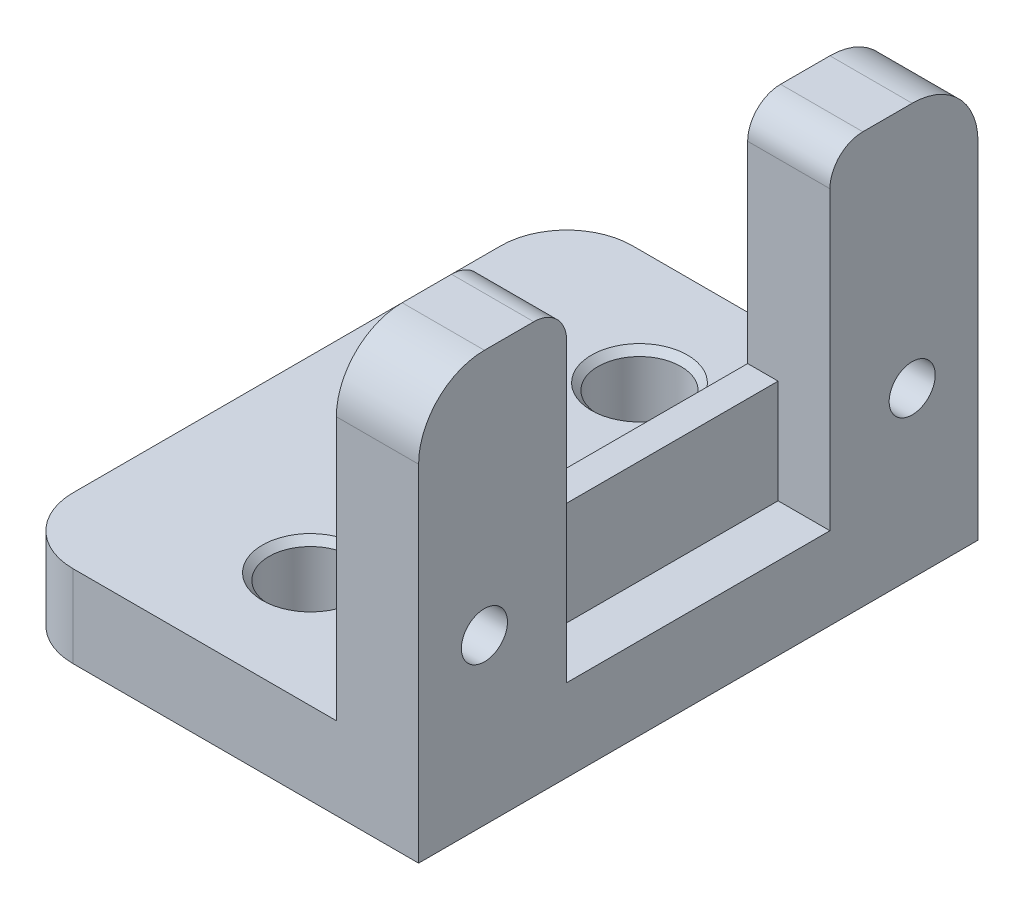
SolidWorks part; units mm, degrees
ref_plane "Plane XZ" through (0, 0, 0) normal (0, 0, 1) x (1, 0, 0)
ref_plane "Plane XY" through (0, 0, 0) normal (0, 1, 0) x (1, 0, 0)
ref_plane "Plane YZ" through (0, 0, 0) normal (1, 0, 0) x (0, 0, -1)
sketch "Sketch1" plane through (0, 0, 0) normal (0, 0, 1) x (1, 0, 0)
  line L0 (-15.875, 0) -> (0, 0)
  line L1 (0, 0) -> (0, 15.875)
  line L2 (0, 15.875) -> (-3.175, 15.875)
  line L3 (-3.175, 15.875) -> (-3.175, 3.175)
  line L4 (-3.175, 3.175) -> (-15.875, 3.175)
  line L5 (-15.875, 3.175) -> (-15.875, 0)
  dimension "D1" = 15.875
  dimension "D2" = 3.175
extrude "Boss-Extrude1" add sketch "Sketch1" along normal mid plane 21.59
sketch "Sketch2" plane through (0, 0, 0) normal (1, 0, 0) x (0, 0, -1)
  line L0 (0, 0) -> (0, 3.175) construction
  line L1 (-10.795, 0) -> (10.795, 0) construction
  line L2 (-10.795, 15.875) -> (10.795, 15.875) construction
  line L3 (-5.08, 15.875) -> (5.08, 15.875)
  line L4 (-5.08, 15.875) -> (-5.08, 3.175)
  line L5 (-5.08, 3.175) -> (5.08, 3.175)
  line L6 (5.08, 15.875) -> (5.08, 3.175)
  line L7 (-10.795, 3.175) -> (10.795, 3.175) construction
  circle A0 centre (-8.255, 6.35) radius 0.889
  circle A1 centre (8.255, 6.35) radius 0.889
  dimension "D1" = 16.51
  dimension "D2" = 1.778
  dimension "D3" = 3.175
  dimension "D4" = 12.7
  dimension "D5" = 10.16
extrude "Cut-Extrude1" cut sketch "Sketch2" against normal through all
sketch "Sketch3" plane through (0, 3.175, 0) normal (0, 1, 0) x (1, 0, 0)
  line L0 (0, 0) -> (-8.62, 0) construction
  line L1 (0, -5.08) -> (0, 5.08) construction
  line L2 (-8.62, 6.35) -> (-8.62, -6.35) construction
  circle A0 centre (-8.62, 6.35) radius 1.6
  circle A1 centre (-8.62, -6.35) radius 1.6
  dimension "D3" = 3.2
  dimension "D1" = 12.7
  dimension "D2" = 8.62
extrude "Cut-Extrude2" cut sketch "Sketch3" against normal through all
ref_plane "Plane1" through (10, 0, 0) normal (1, 0, 0) x (0, 0, -1)
sketch "Sketch4" plane through (0, 3.175, 0) normal (0, 1, 0) x (1, 0, 0)
  line L0 (-8.112, -6.35) -> (-13.192, -6.35) construction
  line L1 (-8.112, -7.95) -> (-13.192, -7.95)
  line L2 (-8.112, -4.75) -> (-13.192, -4.75)
  line L3 (0, 0) -> (-15.875, 0) construction
  line L4 (-15.875, -10.795) -> (-15.875, 10.795) construction
  line L5 (-8.112, 6.35) -> (-13.192, 6.35) construction
  line L6 (-8.112, 7.95) -> (-13.192, 7.95)
  line L7 (-8.112, 4.75) -> (-13.192, 4.75)
  arc A0 (-8.112, -7.95) -> (-8.112, -4.75) centre (-8.112, -6.35) ccw
  arc A1 (-13.192, -4.75) -> (-13.192, -7.95) centre (-13.192, -6.35) ccw
  circle A2 centre (-8.62, -6.35) radius 1.6 construction
  arc A3 (-8.112, 7.95) -> (-8.112, 4.75) centre (-8.112, 6.35) cw
  arc A4 (-13.192, 4.75) -> (-13.192, 7.95) centre (-13.192, 6.35) cw
  point P2 (-10.652, -6.35)
  point P11 (-8.62, -6.35)
  point P18 (-10.652, 6.35)
  dimension "D1" = 0.508
  dimension "D2" = 5.08
  dimension "D3" = 3.2
sketch "Sketch5" plane through (0, 3.175, 0) normal (0, 1, 0) x (1, 0, 0)
  line L0 (-3.175, 5.08) -> (0, 5.08) construction
  line L1 (-3.175, -5.08) -> (-2, -5.08)
  line L2 (-3.175, -5.08) -> (-3.175, 5.08)
  line L3 (-3.175, 5.08) -> (-2, 5.08)
  line L4 (-2, -5.08) -> (-2, 5.08)
  line L5 (0, -5.08) -> (0, 5.08) construction
  dimension "D1" = 2
extrude "Boss-Extrude2" add sketch "Sketch5" along normal blind 4
chamfer "Chamfer1" distance 0.254 angle 45 2 edges at (-10.22, 3.175, 6.35) (-10.22, 3.175, -6.35)
fillet "Fillet1" radius 2.54 4 edges at (-1.5875, 15.875, -10.795) (-1.5875, 15.875, 10.795) (-15.875, 1.5875, -10.795) (-15.875, 1.5875, 10.795)
fillet "Fillet2" radius 1.27 2 edges at (-1.5875, 15.875, 5.08) (-1.5875, 15.875, -5.08)
